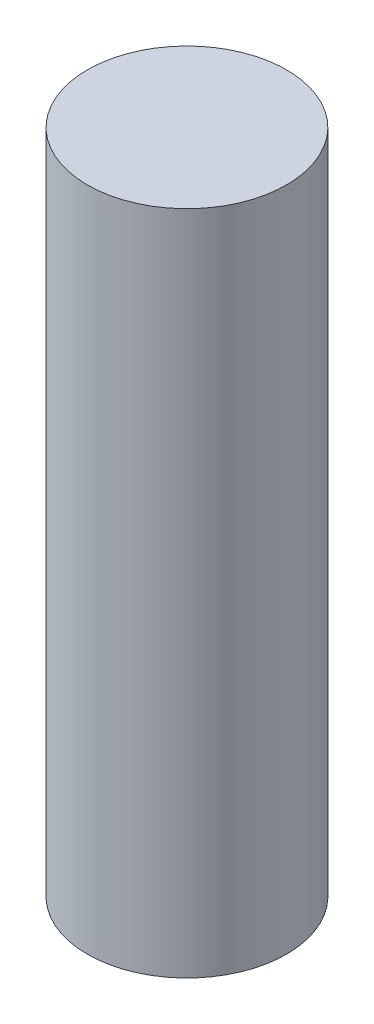
SolidWorks part; units mm, degrees
material "Plain Carbon Steel"
ref_plane "Front Plane" through (0, 0, 0) normal (0, 0, 1) x (1, 0, 0)
ref_plane "Top Plane" through (0, 0, 0) normal (0, 1, 0) x (1, 0, 0)
ref_plane "Right Plane" through (0, 0, 0) normal (1, 0, 0) x (0, 0, -1)
sketch "Sketch1" plane through (0, 0, 0) normal (0, 1, 0) x (1, 0, 0)
  circle A0 centre (0, 0) radius 5
  dimension "D1" = 10
extrude "Boss-Extrude1" add sketch "Sketch1" along normal blind 33.43
